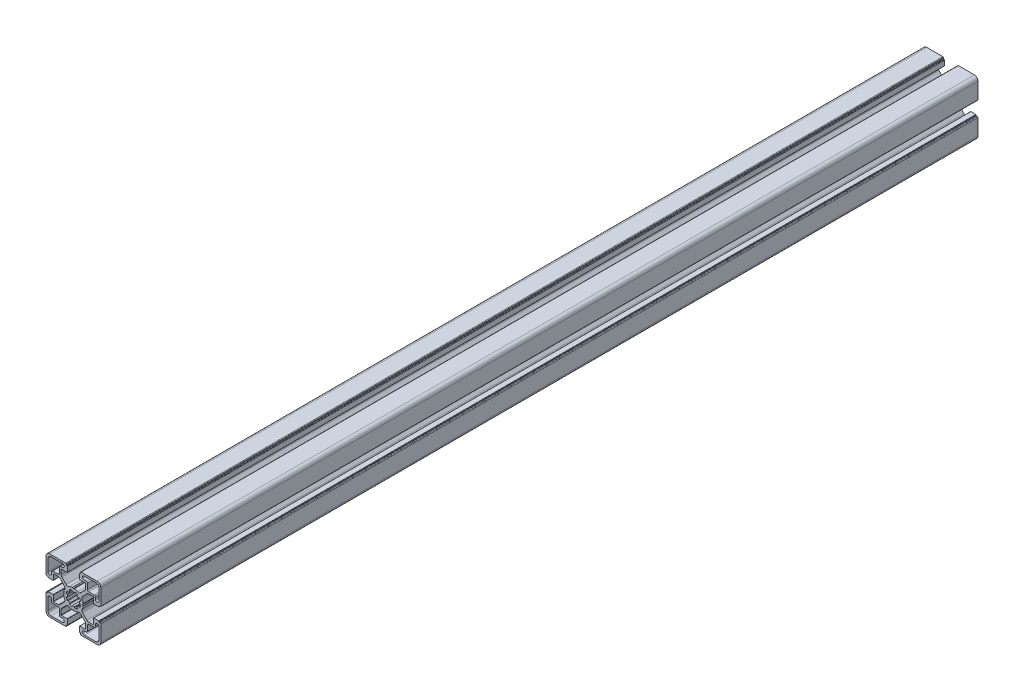
SolidWorks part; units mm, degrees
ref_plane "Plan de face" through (0, 0, 0) normal (0, 0, 1) x (1, 0, 0)
ref_plane "Plan de dessus" through (0, 0, 0) normal (0, 1, 0) x (1, 0, 0)
ref_plane "Plan de droite" through (0, 0, 0) normal (1, 0, 0) x (0, 0, -1)
sketch "Esquisse2" plane through (0, 0, 0) normal (0, 0, 1) x (1, 0, 0)
  line L28 (-195.0842, -352.0697) -> (-194.515, -352.1681)
  line L29 (-195.438, -354.39) -> (-195.9151, -354.0583)
  line L30 (-197.1408, -355.2803) -> (-196.8135, -355.7444)
  line L31 (-199.0372, -356.663) -> (-199.1374, -356.106)
  line L36 (-195.0842, -350.294) -> (-194.515, -350.1956)
  line L37 (-195.438, -347.9737) -> (-195.9151, -348.3053)
  line L38 (-197.1408, -347.0834) -> (-196.8135, -346.6192)
  line L39 (-199.0372, -345.7007) -> (-199.1374, -346.2577)
  line L40 (-200.9723, -356.663) -> (-200.8722, -356.106)
  line L41 (-202.8688, -355.2803) -> (-203.1961, -355.7444)
  line L42 (-204.5715, -354.39) -> (-204.0945, -354.0583)
  line L43 (-204.9253, -352.0697) -> (-205.4945, -352.1681)
  line L44 (-204.9253, -350.294) -> (-205.4945, -350.1956)
  line L45 (-204.5715, -347.9737) -> (-204.0945, -348.3053)
  line L46 (-202.8688, -347.0834) -> (-203.1961, -346.6192)
  line L47 (-200.9723, -345.7007) -> (-200.8722, -346.2577)
  line L105 (-200.0048, -338.2818) -> (-200.0048, -369.1677) construction
  line L107 (-190.0994, -351.1818) -> (-217.4619, -351.1818) construction
  line L108 (-191.0048, -330.1818) -> (-181.5048, -330.1818)
  line L109 (-189.4548, -333.1818) -> (-191.0048, -333.1818)
  line L116 (-221.0047, -332.6818) -> (-221.0047, -342.1816)
  line L117 (-218.0047, -342.1816) -> (-218.0047, -340.6318)
  line L118 (-217.0047, -339.6318) -> (-212.5547, -339.6318)
  line L119 (-211.5547, -338.6318) -> (-211.5547, -334.1818)
  line L120 (-210.5547, -333.1818) -> (-209.0047, -333.1818)
  line L121 (-209.0047, -330.1818) -> (-218.5047, -330.1818)
  line L122 (-188.4548, -338.6318) -> (-188.4548, -334.1818)
  line L123 (-183.0048, -339.6318) -> (-187.4548, -339.6318)
  line L124 (-182.0048, -342.1816) -> (-182.0048, -340.6318)
  line L125 (-179.0048, -332.6818) -> (-179.0048, -342.1816)
  line L126 (-191.0048, -372.1819) -> (-181.5048, -372.1819)
  line L127 (-189.4548, -369.1819) -> (-191.0048, -369.1819)
  line L128 (-188.4548, -363.7319) -> (-188.4548, -368.1819)
  line L129 (-183.0048, -362.7319) -> (-187.4548, -362.7319)
  line L130 (-182.0048, -360.182) -> (-182.0048, -361.7319)
  line L131 (-179.0048, -369.6819) -> (-179.0048, -360.182)
  line L196 (-192.4647, -351.135) -> (-192.0308, -350.3893)
  line L197 (-192.4413, -345.3231) -> (-188.875, -341.7569)
  line L198 (-187.5, -341.1873) -> (-183.6879, -341.1873)
  line L199 (-183.4879, -341.3873) -> (-183.4879, -345.9818)
  line L200 (-183.2879, -346.1818) -> (-179.2852, -346.1818)
  line L201 (-178.9852, -345.8818) -> (-178.9852, -345.6818)
  line L202 (-178.6852, -345.3818) -> (-178.0048, -345.3818)
  line L203 (-177.5048, -344.8818) -> (-177.5048, -331.6818)
  line L204 (-180.5048, -328.6818) -> (-193.6291, -328.6818)
  line L205 (-194.1291, -329.1818) -> (-194.1291, -329.8818)
  line L206 (-194.4291, -330.1818) -> (-194.7048, -330.1818)
  line L207 (-195.0048, -330.4818) -> (-195.0048, -334.515)
  line L208 (-194.8048, -334.715) -> (-190.0994, -334.715)
  line L209 (-189.8994, -334.915) -> (-189.8994, -338.7103)
  line L210 (-190.4852, -340.1245) -> (-194.0599, -343.6992)
  line L211 (-199.25, -343.207) -> (-199.8921, -343.5749)
  line L212 (-200.1174, -343.5749) -> (-200.7595, -343.207)
  line L213 (-205.9497, -343.6992) -> (-209.5244, -340.1245)
  line L214 (-210.1102, -338.7103) -> (-210.1102, -334.915)
  line L215 (-209.9102, -334.715) -> (-205.2048, -334.715)
  line L216 (-205.0048, -334.515) -> (-205.0048, -330.4818)
  line L217 (-205.3048, -330.1818) -> (-205.5805, -330.1818)
  line L218 (-205.8805, -329.8818) -> (-205.8805, -329.1818)
  line L219 (-206.3805, -328.6818) -> (-219.5047, -328.6818)
  line L220 (-222.5047, -331.6818) -> (-222.5047, -344.8818)
  line L221 (-222.0047, -345.3818) -> (-221.3244, -345.3818)
  line L222 (-221.0244, -345.6818) -> (-221.0244, -345.8818)
  line L223 (-220.7244, -346.1818) -> (-216.7217, -346.1818)
  line L224 (-216.5217, -345.9818) -> (-216.5217, -341.3873)
  line L225 (-216.3217, -341.1873) -> (-212.5095, -341.1873)
  line L226 (-211.1345, -341.7569) -> (-207.5682, -345.3231)
  line L227 (-207.9787, -350.3893) -> (-207.5448, -351.135)
  line L228 (-207.5448, -351.2287) -> (-207.9787, -351.9744)
  line L229 (-207.5682, -357.0405) -> (-211.1345, -360.6068)
  line L230 (-212.5095, -361.1764) -> (-216.3217, -361.1764)
  line L231 (-216.5217, -360.9764) -> (-216.5217, -356.3819)
  line L232 (-216.7217, -356.1819) -> (-220.7244, -356.1819)
  line L233 (-221.0244, -356.4819) -> (-221.0244, -356.6818)
  line L234 (-221.3244, -356.9818) -> (-222.0047, -356.9818)
  line L235 (-222.5047, -357.4818) -> (-222.5047, -370.6819)
  line L236 (-219.5047, -373.6819) -> (-206.3805, -373.6819)
  line L237 (-205.8805, -373.1819) -> (-205.8805, -372.4819)
  line L238 (-205.5805, -372.1819) -> (-205.3048, -372.1819)
  line L239 (-205.0048, -371.8819) -> (-205.0048, -367.8487)
  line L240 (-205.2048, -367.6487) -> (-209.9102, -367.6487)
  line L241 (-210.1102, -367.4487) -> (-210.1102, -363.6534)
  line L242 (-209.5244, -362.2392) -> (-205.9497, -358.6645)
  line L243 (-200.7595, -359.1566) -> (-200.1174, -358.7888)
  line L244 (-199.8921, -358.7888) -> (-199.25, -359.1566)
  line L245 (-194.0599, -358.6645) -> (-190.4852, -362.2392)
  line L246 (-189.8994, -363.6534) -> (-189.8994, -367.4487)
  line L247 (-190.0994, -367.6487) -> (-194.8048, -367.6487)
  line L248 (-195.0048, -367.8487) -> (-195.0048, -371.8819)
  line L249 (-194.7048, -372.1819) -> (-194.4291, -372.1819)
  line L250 (-194.1291, -372.4819) -> (-194.1291, -373.1819)
  line L251 (-193.6291, -373.6819) -> (-180.5048, -373.6819)
  line L252 (-177.5048, -370.6819) -> (-177.5048, -357.4818)
  line L253 (-178.0048, -356.9818) -> (-178.6852, -356.9818)
  line L254 (-178.9852, -356.6818) -> (-178.9852, -356.4819)
  line L255 (-179.2852, -356.1819) -> (-183.2879, -356.1819)
  line L256 (-183.4879, -356.3819) -> (-183.4879, -360.9764)
  line L257 (-183.6879, -361.1764) -> (-187.5, -361.1764)
  line L258 (-188.875, -360.6068) -> (-192.4413, -357.0405)
  line L259 (-192.0308, -351.9744) -> (-192.4647, -351.2287)
  line L260 (-209.0047, -372.1819) -> (-218.5047, -372.1819)
  line L261 (-210.5547, -369.1819) -> (-209.0047, -369.1819)
  line L262 (-211.5547, -363.7319) -> (-211.5547, -368.1819)
  line L263 (-217.0047, -362.7319) -> (-212.5547, -362.7319)
  line L264 (-218.0047, -360.182) -> (-218.0047, -361.7319)
  line L265 (-221.0047, -369.6819) -> (-221.0047, -360.182)
  arc A63 (-194.515, -352.1681) -> (-194.0979, -352.793) centre (-194.5809, -352.6637) cw
  arc A64 (-194.0979, -352.793) -> (-194.7023, -354.2383) centre (-199.9813, -351.1818) cw
  arc A65 (-194.7023, -354.2383) -> (-195.438, -354.39) centre (-195.1368, -353.9909) cw
  arc A66 (-195.9151, -354.0583) -> (-197.1408, -355.2803) centre (-200.0048, -351.1818) cw
  arc A67 (-196.8135, -355.7444) -> (-196.9604, -356.4813) centre (-197.2105, -356.0483) cw
  arc A68 (-196.9604, -356.4813) -> (-198.4097, -357.0759) centre (-199.9813, -351.1818) cw
  arc A69 (-198.4097, -357.0759) -> (-199.0372, -356.663) centre (-198.5421, -356.5938) cw
  arc A70 (-199.1374, -356.106) -> (-200.8722, -356.106) centre (-200.0048, -351.1818) cw
  arc A71 (-201.5998, -357.0759) -> (-200.9723, -356.663) centre (-201.4675, -356.5938) ccw
  arc A81 (-195.0842, -352.0697) -> (-195.0842, -350.294) centre (-200.0048, -351.1818) ccw
  arc A82 (-194.515, -350.1956) -> (-194.0979, -349.5706) centre (-194.5809, -349.7) ccw
  arc A83 (-194.0979, -349.5706) -> (-194.7023, -348.1254) centre (-199.9813, -351.1818) ccw
  arc A84 (-194.7023, -348.1254) -> (-195.438, -347.9737) centre (-195.1368, -348.3728) ccw
  arc A85 (-195.9151, -348.3053) -> (-197.1408, -347.0834) centre (-200.0048, -351.1818) ccw
  arc A86 (-196.8135, -346.6192) -> (-196.9604, -345.8824) centre (-197.2105, -346.3153) ccw
  arc A87 (-196.9604, -345.8824) -> (-198.4097, -345.2878) centre (-199.9813, -351.1818) ccw
  arc A88 (-198.4097, -345.2878) -> (-199.0372, -345.7007) centre (-198.5421, -345.7699) ccw
  arc A89 (-199.1374, -346.2577) -> (-200.8722, -346.2577) centre (-200.0048, -351.1818) ccw
  arc A90 (-203.0492, -356.4813) -> (-201.5998, -357.0759) centre (-200.0282, -351.1818) ccw
  arc A91 (-203.1961, -355.7444) -> (-203.0492, -356.4813) centre (-202.799, -356.0483) ccw
  arc A92 (-204.0945, -354.0583) -> (-202.8688, -355.2803) centre (-200.0048, -351.1818) ccw
  arc A93 (-205.3073, -354.2383) -> (-204.5715, -354.39) centre (-204.8728, -353.9909) ccw
  arc A94 (-205.9116, -352.793) -> (-205.3073, -354.2383) centre (-200.0282, -351.1818) ccw
  arc A95 (-205.4945, -352.1681) -> (-205.9116, -352.793) centre (-205.4286, -352.6637) ccw
  arc A96 (-204.9253, -352.0697) -> (-204.9253, -350.294) centre (-200.0048, -351.1818) cw
  arc A97 (-205.4945, -350.1956) -> (-205.9116, -349.5706) centre (-205.4286, -349.7) cw
  arc A98 (-205.9116, -349.5706) -> (-205.3073, -348.1254) centre (-200.0282, -351.1818) cw
  arc A99 (-205.3073, -348.1254) -> (-204.5715, -347.9737) centre (-204.8728, -348.3728) cw
  arc A100 (-204.0945, -348.3053) -> (-202.8688, -347.0834) centre (-200.0048, -351.1818) cw
  arc A101 (-203.1961, -346.6192) -> (-203.0492, -345.8824) centre (-202.799, -346.3153) cw
  arc A102 (-203.0492, -345.8824) -> (-201.5998, -345.2878) centre (-200.0282, -351.1818) cw
  arc A103 (-201.5998, -345.2878) -> (-200.9723, -345.7007) centre (-201.4675, -345.7699) cw
  arc A128 (-181.5048, -330.1818) -> (-179.0048, -332.6818) centre (-181.5048, -332.6818) cw
  arc A129 (-191.0048, -333.1818) -> (-191.0048, -330.1818) centre (-191.0048, -331.6818) cw
  arc A130 (-189.4548, -333.1818) -> (-188.4548, -334.1818) centre (-189.4548, -334.1818) cw
  arc A131 (-187.4548, -339.6318) -> (-188.4548, -338.6318) centre (-187.4548, -338.6318) cw
  arc A132 (-183.0048, -339.6318) -> (-182.0048, -340.6318) centre (-183.0048, -340.6318) cw
  arc A133 (-179.0048, -342.1816) -> (-182.0048, -342.1816) centre (-180.5048, -342.1816) cw
  arc A140 (-221.0047, -342.1816) -> (-218.0047, -342.1816) centre (-219.5047, -342.1816) ccw
  arc A141 (-217.0047, -339.6318) -> (-218.0047, -340.6318) centre (-217.0047, -340.6318) ccw
  arc A142 (-212.5547, -339.6318) -> (-211.5547, -338.6318) centre (-212.5547, -338.6318) ccw
  arc A143 (-210.5547, -333.1818) -> (-211.5547, -334.1818) centre (-210.5547, -334.1818) ccw
  arc A144 (-209.0047, -333.1818) -> (-209.0047, -330.1818) centre (-209.0047, -331.6818) ccw
  arc A145 (-218.5047, -330.1818) -> (-221.0047, -332.6818) centre (-218.5047, -332.6818) ccw
  arc A146 (-191.0048, -369.1819) -> (-191.0048, -372.1819) centre (-191.0048, -370.6819) ccw
  arc A147 (-189.4548, -369.1819) -> (-188.4548, -368.1819) centre (-189.4548, -368.1819) ccw
  arc A148 (-187.4548, -362.7319) -> (-188.4548, -363.7319) centre (-187.4548, -363.7319) ccw
  arc A149 (-183.0048, -362.7319) -> (-182.0048, -361.7319) centre (-183.0048, -361.7319) ccw
  arc A150 (-179.0048, -360.182) -> (-182.0048, -360.182) centre (-180.5048, -360.182) ccw
  arc A151 (-181.5048, -372.1819) -> (-179.0048, -369.6819) centre (-181.5048, -369.6819) ccw
  arc A152 (-218.5047, -372.1819) -> (-221.0047, -369.6819) centre (-218.5047, -369.6819) cw
  arc A153 (-209.0047, -369.1819) -> (-209.0047, -372.1819) centre (-209.0047, -370.6819) cw
  arc A154 (-210.5547, -369.1819) -> (-211.5547, -368.1819) centre (-210.5547, -368.1819) cw
  arc A155 (-212.5547, -362.7319) -> (-211.5547, -363.7319) centre (-212.5547, -363.7319) cw
  arc A156 (-217.0047, -362.7319) -> (-218.0047, -361.7319) centre (-217.0047, -361.7319) cw
  arc A157 (-221.0047, -360.182) -> (-218.0047, -360.182) centre (-219.5047, -360.182) cw
  arc A254 (-192.4647, -351.135) -> (-192.4734, -351.1818) centre (-192.2739, -351.1948) ccw
  arc A255 (-192.0308, -350.3893) -> (-192.0048, -350.2678) centre (-192.2037, -350.2887) ccw
  arc A256 (-192.0048, -350.2678) -> (-192.8044, -347.57) centre (-199.9552, -351.157) ccw
  arc A257 (-192.4413, -345.3231) -> (-192.8044, -347.57) centre (-191.0663, -346.6981) ccw
  arc A258 (-187.5, -341.1873) -> (-188.875, -341.7569) centre (-187.5, -343.1318) ccw
  arc A259 (-183.4879, -341.3873) -> (-183.6879, -341.1873) centre (-183.6879, -341.3873) ccw
  arc A260 (-183.4879, -345.9818) -> (-183.2879, -346.1818) centre (-183.2879, -345.9818) ccw
  arc A261 (-179.2852, -346.1818) -> (-178.9852, -345.8818) centre (-179.2852, -345.8818) ccw
  arc A262 (-178.6852, -345.3818) -> (-178.9852, -345.6818) centre (-178.6852, -345.6818) ccw
  arc A263 (-178.0048, -345.3818) -> (-177.5048, -344.8818) centre (-178.0048, -344.8818) ccw
  arc A264 (-177.5048, -331.6818) -> (-180.5048, -328.6818) centre (-180.5048, -331.6818) ccw
  arc A265 (-193.6291, -328.6818) -> (-194.1291, -329.1818) centre (-193.6291, -329.1818) ccw
  arc A266 (-194.4291, -330.1818) -> (-194.1291, -329.8818) centre (-194.4291, -329.8818) ccw
  arc A267 (-194.7048, -330.1818) -> (-195.0048, -330.4818) centre (-194.7048, -330.4818) ccw
  arc A268 (-195.0048, -334.515) -> (-194.8048, -334.715) centre (-194.8048, -334.515) ccw
  arc A269 (-189.8994, -334.915) -> (-190.0994, -334.715) centre (-190.0994, -334.915) ccw
  arc A270 (-190.4852, -340.1245) -> (-189.8994, -338.7103) centre (-191.8994, -338.7103) ccw
  arc A271 (-196.3383, -344.0086) -> (-194.0599, -343.6992) centre (-195.4193, -342.2322) ccw
  arc A272 (-196.3383, -344.0086) -> (-199.1284, -343.1818) centre (-199.9813, -351.1818) ccw
  arc A273 (-199.1284, -343.1818) -> (-199.25, -343.207) centre (-199.1506, -343.3806) ccw
  arc A274 (-200.0048, -343.6509) -> (-199.8921, -343.5749) centre (-200.0537, -343.457) ccw
  arc A275 (-200.1174, -343.5749) -> (-200.0048, -343.6509) centre (-199.9559, -343.457) ccw
  arc A276 (-200.7595, -343.207) -> (-200.8812, -343.1818) centre (-200.8589, -343.3806) ccw
  arc A277 (-200.8812, -343.1818) -> (-203.6713, -344.0086) centre (-200.0282, -351.1818) ccw
  arc A278 (-205.9497, -343.6992) -> (-203.6713, -344.0086) centre (-204.5903, -342.2322) ccw
  arc A279 (-210.1102, -338.7103) -> (-209.5244, -340.1245) centre (-208.1102, -338.7103) ccw
  arc A280 (-209.9102, -334.715) -> (-210.1102, -334.915) centre (-209.9102, -334.915) ccw
  arc A281 (-205.2048, -334.715) -> (-205.0048, -334.515) centre (-205.2048, -334.515) ccw
  arc A282 (-205.0048, -330.4818) -> (-205.3048, -330.1818) centre (-205.3048, -330.4818) ccw
  arc A283 (-205.8805, -329.8818) -> (-205.5805, -330.1818) centre (-205.5805, -329.8818) ccw
  arc A284 (-205.8805, -329.1818) -> (-206.3805, -328.6818) centre (-206.3805, -329.1818) ccw
  arc A285 (-219.5047, -328.6818) -> (-222.5047, -331.6818) centre (-219.5047, -331.6818) ccw
  arc A286 (-222.5047, -344.8818) -> (-222.0047, -345.3818) centre (-222.0047, -344.8818) ccw
  arc A287 (-221.0244, -345.6818) -> (-221.3244, -345.3818) centre (-221.3244, -345.6818) ccw
  arc A288 (-221.0244, -345.8818) -> (-220.7244, -346.1818) centre (-220.7244, -345.8818) ccw
  arc A289 (-216.7217, -346.1818) -> (-216.5217, -345.9818) centre (-216.7217, -345.9818) ccw
  arc A290 (-216.3217, -341.1873) -> (-216.5217, -341.3873) centre (-216.3217, -341.3873) ccw
  arc A291 (-211.1345, -341.7569) -> (-212.5095, -341.1873) centre (-212.5095, -343.1318) ccw
  arc A292 (-207.2051, -347.57) -> (-207.5682, -345.3231) centre (-208.9432, -346.6981) ccw
  arc A293 (-207.2051, -347.57) -> (-208.0048, -350.2678) centre (-200.0543, -351.157) ccw
  arc A294 (-208.0048, -350.2678) -> (-207.9787, -350.3893) centre (-207.8059, -350.2887) ccw
  arc A295 (-207.5361, -351.1818) -> (-207.5448, -351.135) centre (-207.7357, -351.1948) ccw
  arc A296 (-207.5448, -351.2287) -> (-207.5361, -351.1818) centre (-207.7357, -351.1689) ccw
  arc A297 (-207.9787, -351.9744) -> (-208.0048, -352.0959) centre (-207.8059, -352.075) ccw
  arc A298 (-208.0048, -352.0959) -> (-207.2051, -354.7937) centre (-200.0543, -351.2067) ccw
  arc A299 (-207.5682, -357.0405) -> (-207.2051, -354.7937) centre (-208.9432, -355.6656) ccw
  arc A300 (-212.5095, -361.1764) -> (-211.1345, -360.6068) centre (-212.5095, -359.2319) ccw
  arc A301 (-216.5217, -360.9764) -> (-216.3217, -361.1764) centre (-216.3217, -360.9764) ccw
  arc A302 (-216.5217, -356.3819) -> (-216.7217, -356.1819) centre (-216.7217, -356.3819) ccw
  arc A303 (-220.7244, -356.1819) -> (-221.0244, -356.4819) centre (-220.7244, -356.4819) ccw
  arc A304 (-221.3244, -356.9818) -> (-221.0244, -356.6818) centre (-221.3244, -356.6818) ccw
  arc A305 (-222.0047, -356.9818) -> (-222.5047, -357.4818) centre (-222.0047, -357.4818) ccw
  arc A306 (-222.5047, -370.6819) -> (-219.5047, -373.6819) centre (-219.5047, -370.6819) ccw
  arc A307 (-206.3805, -373.6819) -> (-205.8805, -373.1819) centre (-206.3805, -373.1819) ccw
  arc A308 (-205.5805, -372.1819) -> (-205.8805, -372.4819) centre (-205.5805, -372.4819) ccw
  arc A309 (-205.3048, -372.1819) -> (-205.0048, -371.8819) centre (-205.3048, -371.8819) ccw
  arc A310 (-205.0048, -367.8487) -> (-205.2048, -367.6487) centre (-205.2048, -367.8487) ccw
  arc A311 (-210.1102, -367.4487) -> (-209.9102, -367.6487) centre (-209.9102, -367.4487) ccw
  arc A312 (-209.5244, -362.2392) -> (-210.1102, -363.6534) centre (-208.1102, -363.6534) ccw
  arc A313 (-203.6713, -358.3551) -> (-205.9497, -358.6645) centre (-204.5903, -360.1315) ccw
  arc A314 (-203.6713, -358.3551) -> (-200.8812, -359.1819) centre (-200.0282, -351.1818) ccw
  arc A315 (-200.8812, -359.1819) -> (-200.7595, -359.1566) centre (-200.8589, -358.9831) ccw
  arc A316 (-200.0048, -358.7128) -> (-200.1174, -358.7888) centre (-199.9559, -358.9067) ccw
  arc A317 (-199.8921, -358.7888) -> (-200.0048, -358.7128) centre (-200.0537, -358.9067) ccw
  arc A318 (-199.25, -359.1566) -> (-199.1284, -359.1819) centre (-199.1506, -358.9831) ccw
  arc A319 (-199.1284, -359.1819) -> (-196.3383, -358.3551) centre (-199.9813, -351.1818) ccw
  arc A320 (-194.0599, -358.6645) -> (-196.3383, -358.3551) centre (-195.4193, -360.1315) ccw
  arc A321 (-189.8994, -363.6534) -> (-190.4852, -362.2392) centre (-191.8994, -363.6534) ccw
  arc A322 (-190.0994, -367.6487) -> (-189.8994, -367.4487) centre (-190.0994, -367.4487) ccw
  arc A323 (-194.8048, -367.6487) -> (-195.0048, -367.8487) centre (-194.8048, -367.8487) ccw
  arc A324 (-195.0048, -371.8819) -> (-194.7048, -372.1819) centre (-194.7048, -371.8819) ccw
  arc A325 (-194.1291, -372.4819) -> (-194.4291, -372.1819) centre (-194.4291, -372.4819) ccw
  arc A326 (-194.1291, -373.1819) -> (-193.6291, -373.6819) centre (-193.6291, -373.1819) ccw
  arc A327 (-180.5048, -373.6819) -> (-177.5048, -370.6819) centre (-180.5048, -370.6819) ccw
  arc A328 (-177.5048, -357.4818) -> (-178.0048, -356.9818) centre (-178.0048, -357.4818) ccw
  arc A329 (-178.9852, -356.6818) -> (-178.6852, -356.9818) centre (-178.6852, -356.6818) ccw
  arc A330 (-178.9852, -356.4819) -> (-179.2852, -356.1819) centre (-179.2852, -356.4819) ccw
  arc A331 (-183.2879, -356.1819) -> (-183.4879, -356.3819) centre (-183.2879, -356.3819) ccw
  arc A332 (-183.6879, -361.1764) -> (-183.4879, -360.9764) centre (-183.6879, -360.9764) ccw
  arc A333 (-188.875, -360.6068) -> (-187.5, -361.1764) centre (-187.5, -359.2319) ccw
  arc A334 (-192.8044, -354.7937) -> (-192.4413, -357.0405) centre (-191.0663, -355.6656) ccw
  arc A335 (-192.8044, -354.7937) -> (-192.0048, -352.0959) centre (-199.9552, -351.2067) ccw
  arc A336 (-192.0048, -352.0959) -> (-192.0308, -351.9744) centre (-192.2037, -352.075) ccw
  arc A337 (-192.4734, -351.1818) -> (-192.4647, -351.2287) centre (-192.2739, -351.1689) ccw
extrude "Boss.-Extru.1" add sketch "Esquisse2" along normal blind 720
